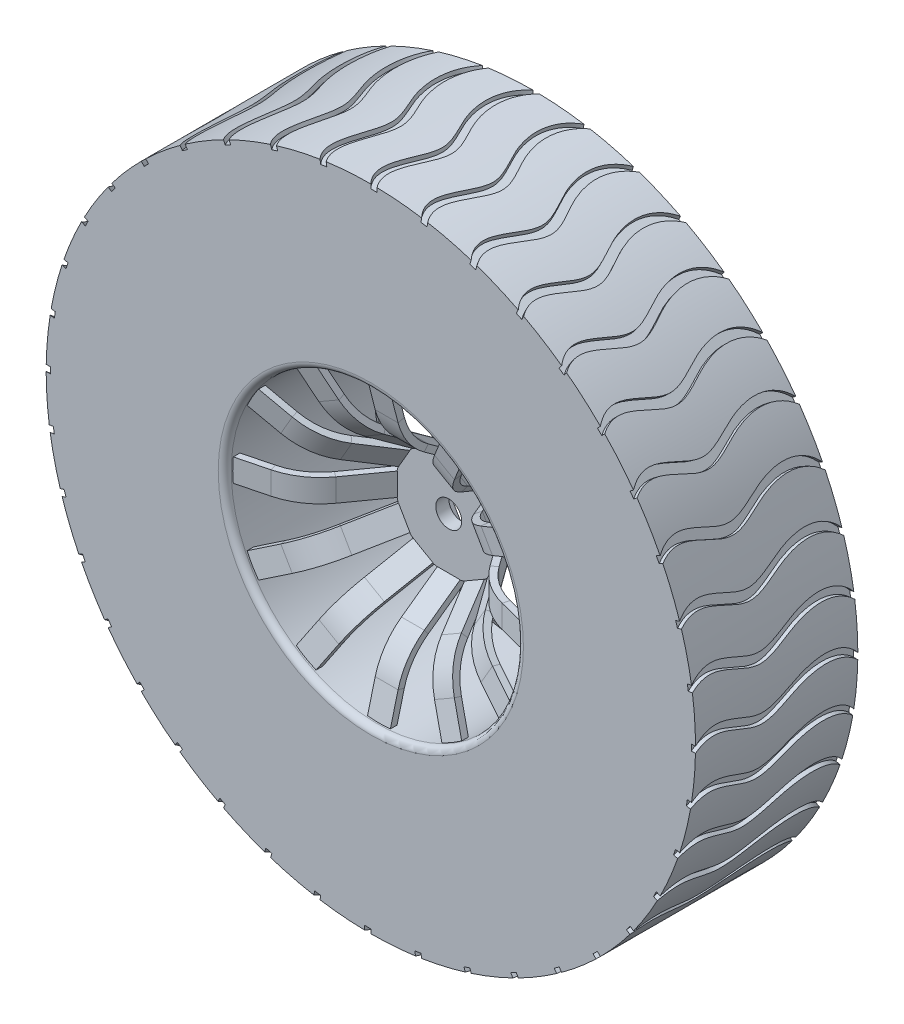
SolidWorks part; units mm, degrees
material "ABS"
ref_plane "Спереди" through (0, 0, 0) normal (0, 0, 1) x (1, 0, 0)
ref_plane "Сверху" through (0, 0, 0) normal (0, 1, 0) x (1, 0, 0)
ref_plane "Справа" through (0, 0, 0) normal (1, 0, 0) x (0, 0, -1)
sketch "Эскиз1" plane through (0, 0, 0) normal (0, 0, 1) x (1, 0, 0)
  circle A0 centre (0, 0) radius 8.15
extrude "Бобышка-Вытянуть1" add sketch "Эскиз1" along normal blind 6
sketch "Эскиз2" plane through (0, 0, 6) normal (0, 0, 1) x (1, 0, 0)
  circle A0 centre (0, 0) radius 2
  dimension "D1" = 4
extrude "Вырез-Вытянуть1" cut sketch "Эскиз2" against normal blind 6
sketch "Эскиз3" plane through (0, 0, 0) normal (0, 0, -1) x (-1, 0, 0)
  line L1 (-7.6788, 0) -> (-3.8394, -6.65)
  line L2 (-3.8394, -6.65) -> (3.8394, -6.65)
  line L3 (3.8394, -6.65) -> (7.6788, 0)
  line L4 (7.6788, 0) -> (3.8394, 6.65)
  line L5 (3.8394, 6.65) -> (-3.8394, 6.65)
  line L6 (-3.8394, 6.65) -> (-7.6788, 0)
  circle A0 centre (0, 0) radius 6.65 construction
extrude "Вырез-Вытянуть2" cut sketch "Эскиз3" against normal blind 4
ref_plane "Плоскость1" through (0, 0, 18) normal (0, 0, 1) x (1, 0, 0)
sketch "Эскиз4" plane through (0, 0, 18) normal (0, 0, 1) x (1, 0, 0)
  circle A0 centre (0, 0) radius 50
  circle A1 centre (0, 0) radius 22.5
  dimension "D1" = 100
  dimension "D2" = 45
extrude "Бобышка-Вытянуть2" add sketch "Эскиз4" against normal blind 25 separate body
sketch "Эскиз5" plane through (0, 0, 0) normal (1, 0, 0) x (0, 0, -1)
  line L0 (-6, 8.15) -> (-6, -8.15) construction
  line L1 (-5, -1.76) -> (-6, -1.76)
  line L2 (-5, -1.76) -> (-5, 1.76)
  line L3 (-5, 1.76) -> (-6, 1.76)
  line L4 (-6, -1.76) -> (-6, 1.76)
  line L5 (-5, -1.76) -> (-6, 1.76) construction
  line L6 (-5, 1.76) -> (-6, -1.76) construction
  point P0 (-5.5, 0)
  dimension "D1" = 3.52
  dimension "D2" = 1
sketch "Эскиз6" plane through (0, 0, 0) normal (0, 1, 0) x (1, 0, 0)
  line L0 (-2.0218, -5.5) -> (-8.1679, -5.5)
  line L1 (-8.1679, -5.5) -> (-12.2811, -11.2267)
  line L2 (-17.9249, -15.0811) -> (-23.2538, -16.4443)
  line L3 (-2.0218, -5.5) -> (0, -5.5)
  arc A0 (-17.9249, -15.0811) -> (-12.2811, -11.2267) centre (-20.4032, -5.3931) ccw
  dimension "D1" = 10
sweep "По траектории2" add profiles "Эскиз5" path "Эскиз6"
pattern_circular "Круговой массив1" count 12 over 360 about axis through (0, 0, 0) along (0, 0, 1) of "По траектории2"
sketch "Эскиз7" plane through (0, 0, 5) normal (0, 0, -1) x (-1, 0, 0)
  circle A0 centre (0, 0) radius 2
extrude "Вырез-Вытянуть3" cut sketch "Эскиз7" against normal blind 25
fillet "Скругление1" radius 1 1 edges at (22.5, 0, 18)
chamfer "Фаска1" distance 2 angle 45 1 edges at (22.5, 0, -7)
sketch "Эскиз8" plane through (0, 0, -7) normal (0, 0, -1) x (-1, 0, 0)
  circle A0 centre (0, 0) radius 26
  circle A1 centre (0, 0) radius 32.5
  dimension "D1" = 65
extrude "Бобышка-Вытянуть3" add sketch "Эскиз8" against normal up to surface (25 mm away) up to face at (23.5, 0, 18)
ref_plane "Плоскость2" through (0, 33.35, 0) normal (0, 1, 0) x (1, 0, 0)
sketch "Эскиз9" plane through (0, 33.35, 0) normal (0, 1, 0) x (1, 0, 0)
  line L0 (32.5, 7) -> (-32.5, 7) construction
  line L1 (-8.965, -18) -> (8.965, -18) construction
  line L2 (0, 7) -> (0.949, 7)
  line L3 (0, -18) -> (0.949, -18)
  spline S0 degree 3 poles (0, 7) (-2.9144, 4.6663) (-2.6828, -1.0803) (2.8897, -8.9836) (-3.3919, -14.4455) (0, -18) knots 0 0 0 0 0.372359 0.594016 1 1 1 1
  spline S1 degree 3 poles (0.949, 7) (-1.4848, 4.4567) (-1.2728, -1.1456) (4.4298, -8.9519) (-1.8054, -14.3946) (0.949, -18) knots 0 0 0 0 0.368016 0.592618 1 1 1 1
extrude "Вырез-Вытянуть4" cut sketch "Эскиз9" against normal blind 3 from offset 19
pattern_circular "Круговой массив2" count 40 over 360 of "Вырез-Вытянуть4"
